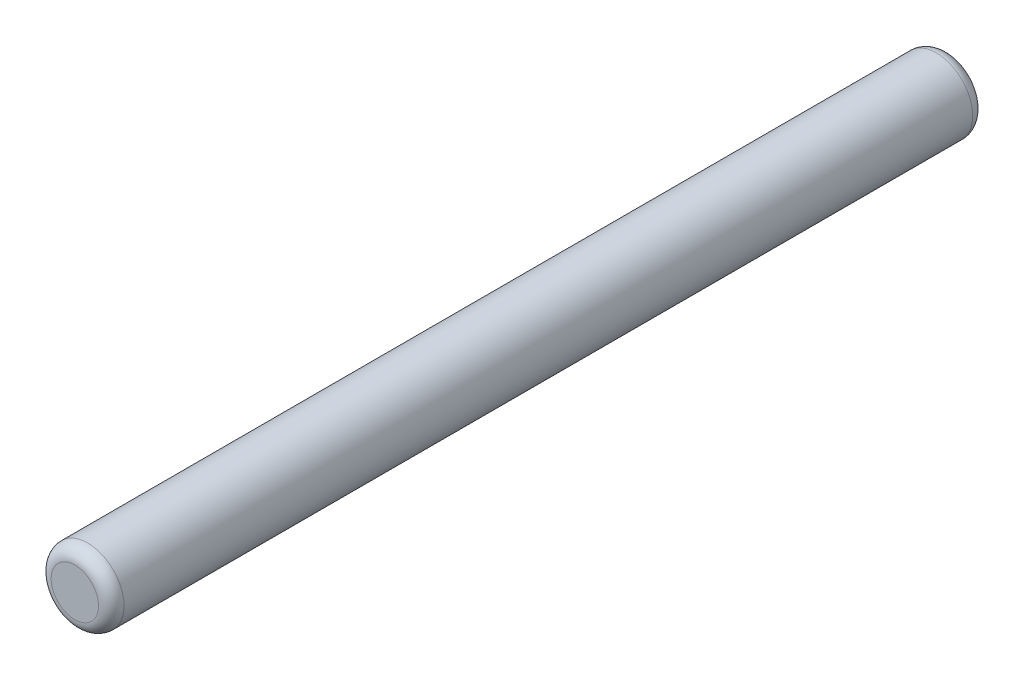
SolidWorks part; units mm, degrees
ref_plane "Front" through (0, 0, 0) normal (0, 0, 1) x (1, 0, 0)
ref_plane "Top" through (0, 0, 0) normal (0, 1, 0) x (1, 0, 0)
ref_plane "Right" through (0, 0, 0) normal (1, 0, 0) x (0, 0, -1)
sketch "Sketch1" plane through (0, 0, 0) normal (0, 0, 1) x (1, 0, 0)
  circle A0 centre (0, 0) radius 1
  dimension "D1" = 2
extrude "Boss-Extrude1" add sketch "Sketch1" along normal mid plane 24
fillet "Fillet1" radius 0.35 2 edges at (1, 0, -12) (1, 0, 12)
